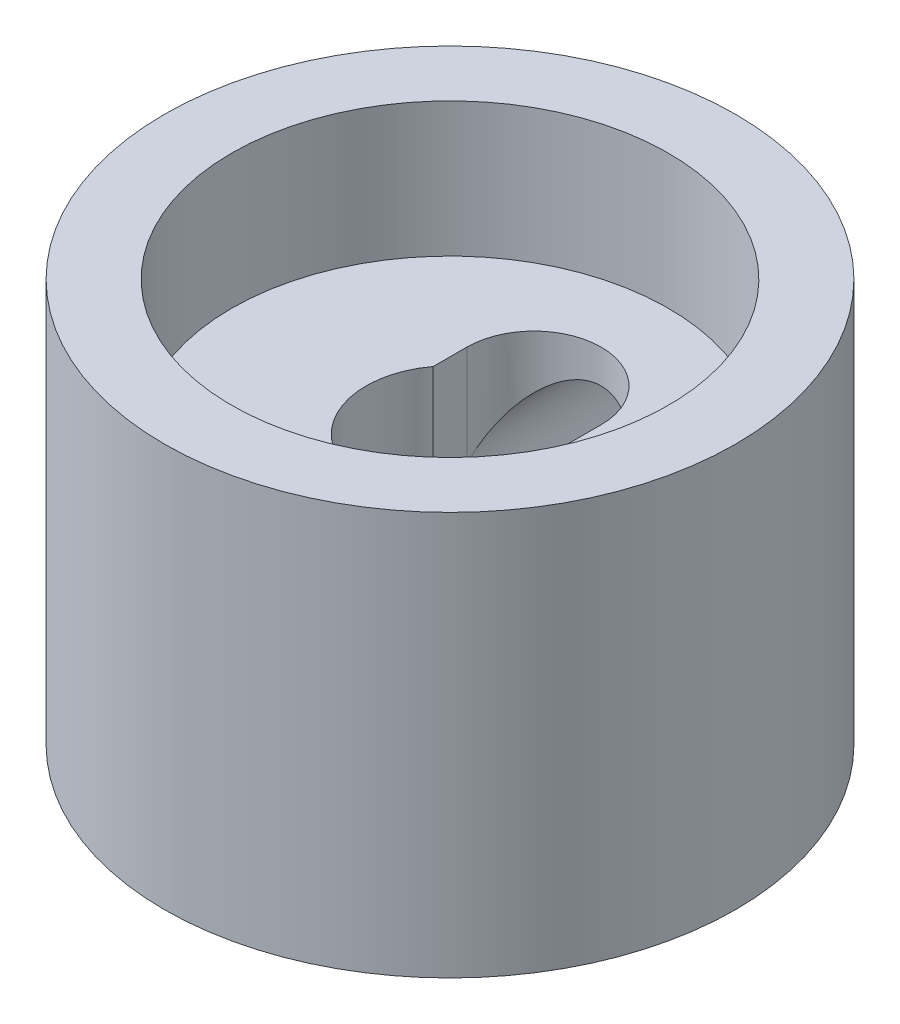
SolidWorks part; units mm, degrees
ref_plane "Front Plane" through (0, 0, 0) normal (0, 0, 1) x (1, 0, 0)
ref_plane "Top Plane" through (0, 0, 0) normal (0, 1, 0) x (1, 0, 0)
ref_plane "Right Plane" through (0, 0, 0) normal (1, 0, 0) x (0, 0, -1)
sketch "Sketch1" plane through (0, 0, 0) normal (0, 0, 1) x (1, 0, 0)
  line L0 (0, 0) -> (12.7, 0)
  line L1 (12.7, 0) -> (12.7, 3.175)
  line L2 (12.7, 3.175) -> (53.975, 3.175)
  line L3 (53.975, 3.175) -> (53.975, 79.375)
  line L4 (53.975, 79.375) -> (41.275, 79.375)
  line L5 (41.275, 79.375) -> (41.275, 53.975)
  line L6 (41.275, 53.975) -> (15.875, 53.975)
  line L7 (15.875, 53.975) -> (15.875, 22.225)
  line L8 (15.875, 22.225) -> (0, 22.225)
  line L9 (0, 22.225) -> (0, 0)
  dimension "D1" = 15.875
  dimension "D2" = 12.7
  dimension "D3" = 3.175
  dimension "D4" = 53.975
  dimension "D5" = 25.4
  dimension "D6" = 31.75
  dimension "D7" = 41.275
  dimension "D8" = 19.05
revolve "Revolve1" add sketch "Sketch1" angle 360 about L9
ref_plane "Plane1" through (0, 0, -53.975) normal (0, 0, -1) x (-1, 0, 0)
sketch "Sketch3" plane through (0, 0, -53.975) normal (0, 0, -1) x (-1, 0, 0)
  line L2 (0, 47.625) -> (0, 22.225) construction
  line L3 (0, 22.225) -> (0, 3.175) construction
  line L4 (0, 3.175) -> (0, 0) construction
  circle A0 centre (0, 34.925) radius 12.7
  point P5 (0, 38.3215)
  point P8 (0, 34.925)
  point P9 (0, 66.5313)
  point P10 (0, 0)
  dimension "D1" = 25.4
  dimension "D2" = 19.05
  dimension "D3" = 25.4
  dimension "D4" = 3.175
extrude "Cut-Extrude1" cut sketch "Sketch3" against normal blind 48.768
sketch "Sketch4" plane through (0, 53.975, 0) normal (0, 1, 0) x (1, 0, 0)
  line L0 (-12.7, 15.875) -> (-12.7, 0)
  line L1 (-12.7, 0) -> (12.7, 0)
  line L2 (12.7, 0) -> (12.7, 15.875)
  arc A0 (12.7, 15.875) -> (-12.7, 15.875) centre (0, 15.875) ccw
  circle A2 centre (0, 0) radius 15.875 construction
  point P1 (0, 23.8081)
  dimension "D1" = 25.4
extrude "Cut-Extrude2" cut sketch "Sketch4" against normal blind 19.05
